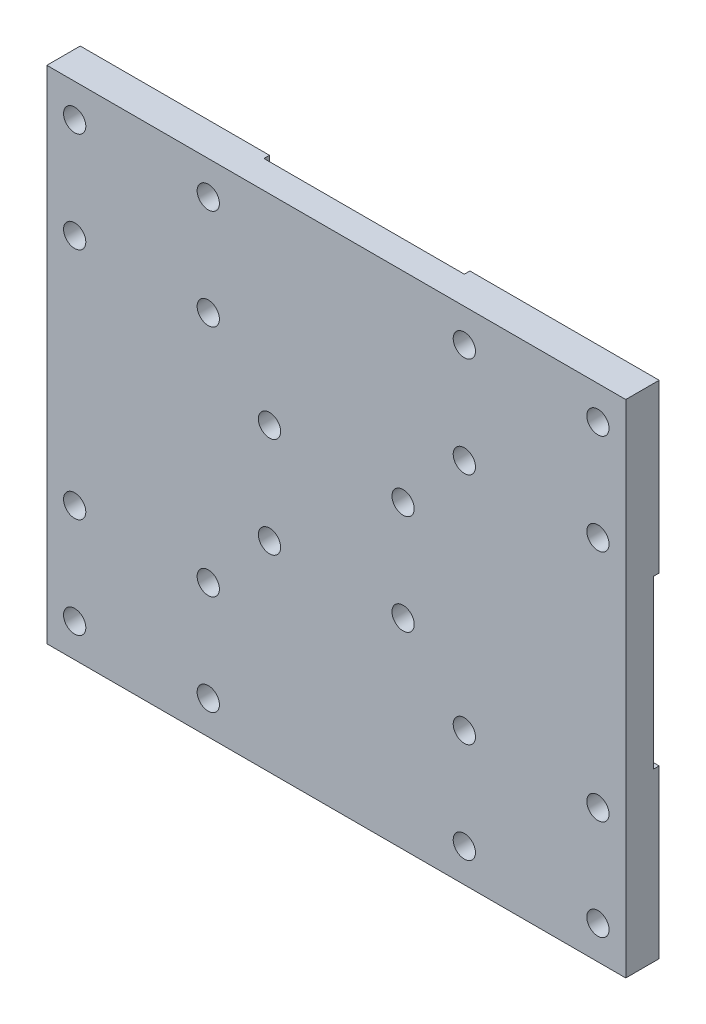
SolidWorks part; units mm, degrees
ref_plane "Alzado" through (0, 0, 0) normal (0, 0, 1) x (1, 0, 0)
ref_plane "Planta" through (0, 0, 0) normal (0, 1, 0) x (1, 0, 0)
ref_plane "Vista lateral" through (0, 0, 0) normal (1, 0, 0) x (0, 0, -1)
sketch "Croquis1" plane through (0, 0, 0) normal (0, 0, 1) x (1, 0, 0)
  line L1 (-52, -45) -> (52, -45)
  line L2 (-52, -45) -> (-52, 45)
  line L3 (-52, 45) -> (52, 45)
  line L4 (52, -45) -> (52, 45)
  line L5 (-52, -45) -> (52, 45) construction
  line L6 (-52, 45) -> (52, -45) construction
  point P0 (0, 0)
  dimension "D1" = 104
  dimension "D2" = 90
extrude "Saliente-Extruir1" add sketch "Croquis1" along normal blind 5
sketch "Croquis3" plane through (0, 0, 0) normal (0, 0, -1) x (-1, 0, 0)
  line L0 (-52, 0) -> (52, 0) construction
  line L1 (-52, 45) -> (-18, 45)
  line L2 (-52, 45) -> (-52, 15)
  line L3 (-52, 15) -> (-18, 15)
  line L4 (-18, 45) -> (-18, 15)
  line L5 (-52, 45) -> (-18, 15) construction
  line L6 (-52, 15) -> (-18, 45) construction
  line L7 (-52, -45) -> (-52, 45) construction
  line L8 (52, 45) -> (52, -45) construction
  line L9 (0, 45) -> (0, -45) construction
  line L10 (-52, 45) -> (52, 45) construction
  line L11 (52, -45) -> (-52, -45) construction
  line L12 (-52, -15) -> (-18, -15)
  line L13 (-18, -45) -> (-18, -15)
  line L14 (-52, -45) -> (-18, -45)
  line L15 (-52, -45) -> (-52, -15)
  line L16 (52, 15) -> (18, 15)
  line L17 (18, 45) -> (18, 15)
  line L18 (52, 45) -> (18, 45)
  line L19 (52, 45) -> (52, 15)
  line L20 (52, -45) -> (52, -15)
  line L21 (52, -45) -> (18, -45)
  line L22 (18, -45) -> (18, -15)
  line L23 (52, -15) -> (18, -15)
  point P0 (-35, 30)
  dimension "D1" = 34
  dimension "D2" = 30
  dimension "D3" = 35
  dimension "D4" = 30
extrude "Saliente-Extruir2" add sketch "Croquis3" along normal blind 1
sketch "Sketch1" plane through (0, 0, 0) normal (0, 0, -1) x (-1, 0, 0)
  circle A0 centre (-47, 39) radius 2
  circle A1 centre (-23, 39) radius 2
  circle A2 centre (-47, 21) radius 2
  circle A3 centre (-23, 21) radius 2
  circle A4 centre (23, 39) radius 2
  circle A5 centre (23, 21) radius 2
  circle A6 centre (47, 21) radius 2
  circle A7 centre (47, 39) radius 2
  circle A8 centre (23, -21) radius 2
  circle A9 centre (23, -39) radius 2
  circle A10 centre (47, -39) radius 2
  circle A11 centre (47, -21) radius 2
  circle A12 centre (-23, -21) radius 2
  circle A13 centre (-23, -39) radius 2
  circle A14 centre (-47, -39) radius 2
  circle A15 centre (-47, -21) radius 2
  circle A16 centre (-12, 9) radius 2
  circle A17 centre (-12, -9) radius 2
  circle A18 centre (12, -9) radius 2
  circle A19 centre (12, 9) radius 2
  dimension "D1" = 4
  dimension "D2" = 4
  dimension "D3" = 4
  dimension "D4" = 4
  dimension "D5" = 4
  dimension "D6" = 4
  dimension "D7" = 4
  dimension "D8" = 4
  dimension "D9" = 4
  dimension "D10" = 4
  dimension "D11" = 4
  dimension "D12" = 4
  dimension "D13" = 4
  dimension "D14" = 4
  dimension "D15" = 4
  dimension "D16" = 4
  dimension "D17" = 4
  dimension "D18" = 4
  dimension "D19" = 4
  dimension "D20" = 4
extrude "Cut-Extrude1" cut sketch "Sketch1" against normal up to surface (5 mm away) up to face at (0, 0, 5)
